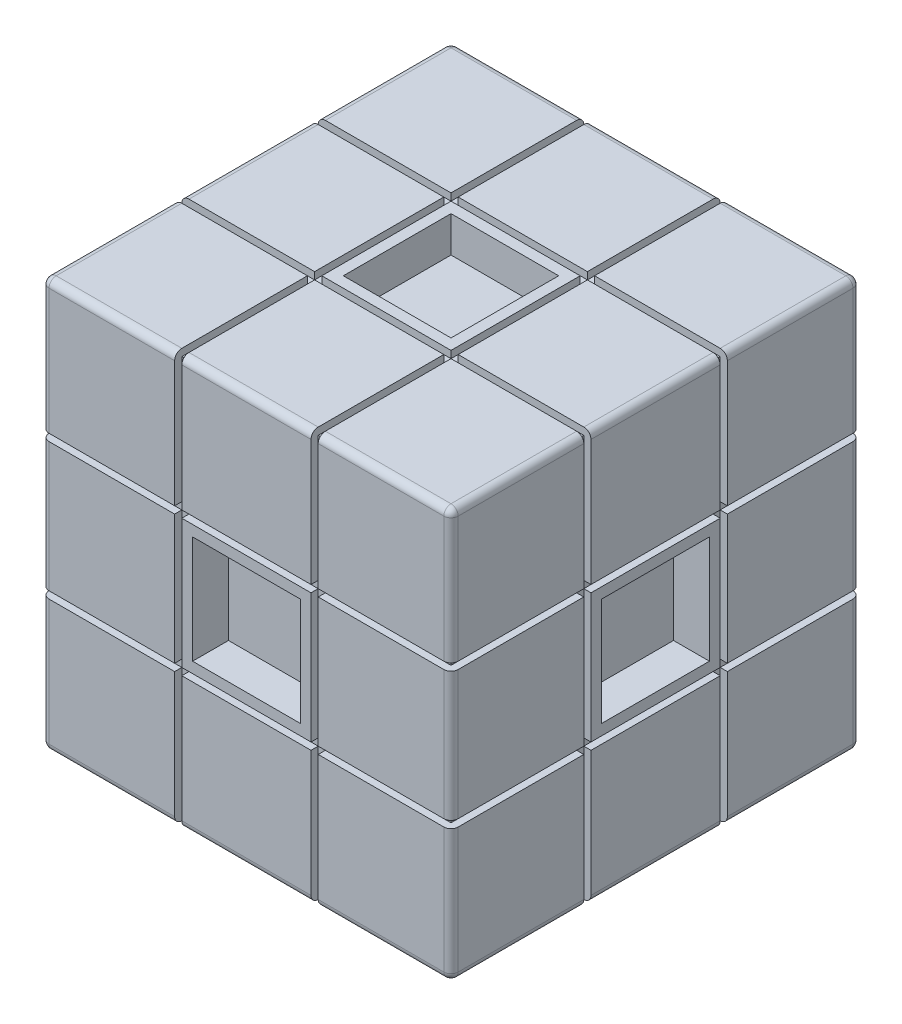
SolidWorks part; units mm, degrees
ref_plane "前视基准面" through (0, 0, 0) normal (0, 0, 1) x (1, 0, 0)
ref_plane "上视基准面" through (0, 0, 0) normal (0, 1, 0) x (1, 0, 0)
ref_plane "右视基准面" through (0, 0, 0) normal (1, 0, 0) x (0, 0, -1)
sketch "草图1" plane through (0, 0, 0) normal (0, 1, 0) x (1, 0, 0)
  line L0 (0, 0) -> (57, 0)
  line L1 (0, 0) -> (0, 57)
  line L2 (57, 0) -> (57, 57)
  line L3 (0, 57) -> (57, 57)
extrude "凸台-拉伸1" add sketch "草图1" along normal blind 57
sketch "草图2" plane through (0, 0, 0) normal (0, 1, 0) x (1, 0, 0)
  line L0 (36, 21) -> (36, 36)
  line L1 (36, 21) -> (21, 21)
  line L2 (36, 36) -> (21, 36)
  line L3 (21, 21) -> (21, 36)
  point P1 (28.5, 28.5)
extrude "切除-拉伸3" cut sketch "草图2" along normal blind 5
sketch "草图5" plane through (0, 0, 0) normal (0, 0, 1) x (1, 0, 0)
  line L0 (36, 36) -> (36, 21)
  line L1 (36, 36) -> (21, 36)
  line L2 (36, 21) -> (21, 21)
  line L3 (21, 36) -> (21, 21)
  point P1 (28.5, 28.5)
extrude "切除-拉伸4" cut sketch "草图5" against normal blind 5
sketch "草图6" plane through (0, 57, 0) normal (0, 1, 0) x (1, 0, 0)
  line L0 (36, 36) -> (36, 21)
  line L1 (36, 36) -> (21, 36)
  line L2 (36, 21) -> (21, 21)
  line L3 (21, 36) -> (21, 21)
extrude "切除-拉伸5" cut sketch "草图6" against normal blind 5
sketch "草图8" plane through (0, 0, -57) normal (0, 0, -1) x (-1, 0, 0)
  line L0 (-36, 21) -> (-36, 36)
  line L1 (-36, 21) -> (-21, 21)
  line L2 (-36, 36) -> (-21, 36)
  line L3 (-21, 21) -> (-21, 36)
extrude "切除-拉伸6" cut sketch "草图8" against normal blind 5
sketch "草图9" plane through (0, 0, 0) normal (-1, 0, 0) x (0, 0, 1)
  line L0 (-36, 36) -> (-21, 36)
  line L1 (-36, 36) -> (-36, 21)
  line L2 (-21, 36) -> (-21, 21)
  line L3 (-36, 21) -> (-21, 21)
extrude "切除-拉伸7" cut sketch "草图9" against normal blind 5
sketch "草图10" plane through (57, 0, 0) normal (1, 0, 0) x (0, 0, -1)
  line L0 (21, 36) -> (36, 36)
  line L1 (21, 36) -> (21, 21)
  line L2 (36, 36) -> (36, 21)
  line L3 (21, 21) -> (36, 21)
extrude "切除-拉伸8" cut sketch "草图10" against normal blind 5
sketch "草图12" plane through (0, 0, 0) normal (0, 0, 1) x (1, 0, 0)
  line L0 (38.5, 57) -> (38.5, 38.5)
  line L1 (0, 38.5) -> (0, 37.5)
  line L2 (0, 18.5) -> (0, 19.5)
  line L3 (57, 37.5) -> (57, 38.5)
  line L4 (57, 19.5) -> (57, 18.5)
  line L5 (37.5, 57) -> (37.5, 38.5)
  line L6 (57, 18.5) -> (38.5, 18.5)
  line L7 (37.5, 57) -> (38.5, 57)
  line L8 (38.5, 0) -> (37.5, 0)
  line L9 (18.5, 0) -> (19.5, 0)
  line L10 (19.5, 57) -> (18.5, 57)
  line L11 (19.5, 57) -> (19.5, 38.5)
  line L12 (18.5, 57) -> (18.5, 38.5)
  line L13 (18.5, 37.5) -> (0, 37.5)
  line L14 (57, 19.5) -> (38.5, 19.5)
  line L15 (57, 37.5) -> (38.5, 37.5)
  line L16 (57, 38.5) -> (38.5, 38.5)
  line L17 (18.5, 38.5) -> (0, 38.5)
  line L18 (18.5, 37.5) -> (18.5, 19.5)
  line L19 (19.5, 37.5) -> (19.5, 19.5)
  line L20 (37.5, 37.5) -> (37.5, 19.5)
  line L21 (38.5, 37.5) -> (38.5, 19.5)
  line L22 (37.5, 38.5) -> (19.5, 38.5)
  line L23 (37.5, 37.5) -> (19.5, 37.5)
  line L24 (38.5, 18.5) -> (38.5, 0)
  line L25 (37.5, 18.5) -> (37.5, 0)
  line L26 (37.5, 19.5) -> (19.5, 19.5)
  line L27 (37.5, 18.5) -> (19.5, 18.5)
  line L28 (18.5, 18.5) -> (18.5, 0)
  line L29 (19.5, 18.5) -> (19.5, 0)
  line L30 (18.5, 19.5) -> (0, 19.5)
  line L31 (18.5, 18.5) -> (0, 18.5)
extrude "切除-拉伸9" cut sketch "草图12" against normal blind 1
sketch "草图13" plane through (0, 0, 0) normal (0, 0, 1) x (1, 0, 0)
  line L0 (18.5, 57) -> (19.5, 57)
  line L1 (18.5, 57) -> (18.5, 56)
  line L2 (18.5, 57) -> (18.5, 38.5) construction
  line L3 (18.5, 56) -> (19.5, 56)
  line L4 (19.5, 38.5) -> (19.5, 57) construction
  line L5 (19.5, 56) -> (19.5, 57)
  line L9 (37.5, 56) -> (37.5, 57)
  line L10 (38.5, 56) -> (37.5, 56)
  line L11 (38.5, 57) -> (38.5, 56)
  line L12 (38.5, 57) -> (37.5, 57)
  line L15 (38.5, 0) -> (37.5, 0)
  line L16 (38.5, 0) -> (38.5, 1)
  line L17 (38.5, 1) -> (37.5, 1)
  line L18 (37.5, 1) -> (37.5, 0)
  line L19 (19.5, 1) -> (19.5, 0)
  line L20 (18.5, 1) -> (19.5, 1)
  line L21 (18.5, 0) -> (18.5, 1)
  line L22 (18.5, 0) -> (19.5, 0)
  line L23 (0, 18.5) -> (0, 19.5)
  line L24 (0, 18.5) -> (1, 18.5)
  line L25 (1, 18.5) -> (1, 19.5)
  line L26 (1, 19.5) -> (0, 19.5)
  line L27 (1, 37.5) -> (0, 37.5)
  line L28 (1, 38.5) -> (1, 37.5)
  line L29 (0, 38.5) -> (1, 38.5)
  line L30 (0, 38.5) -> (0, 37.5)
  line L31 (57, 38.5) -> (57, 37.5)
  line L32 (57, 38.5) -> (56, 38.5)
  line L33 (56, 38.5) -> (56, 37.5)
  line L34 (56, 37.5) -> (57, 37.5)
  line L35 (56, 19.5) -> (57, 19.5)
  line L36 (56, 18.5) -> (56, 19.5)
  line L37 (57, 18.5) -> (56, 18.5)
  line L38 (57, 18.5) -> (57, 19.5)
extrude "切除-拉伸10" cut sketch "草图13" against normal through all
sketch "草图14" plane through (0, 0, 0) normal (-1, 0, 0) x (0, 0, 1)
  line L0 (-57, 37.5) -> (-57, 38.5)
  line L1 (-57, 37.5) -> (-56, 37.5)
  line L2 (-57, 38.5) -> (-56, 38.5)
  line L3 (-56, 37.5) -> (-56, 38.5)
  line L7 (-56, 19.5) -> (-56, 18.5)
  line L8 (-57, 18.5) -> (-56, 18.5)
  line L9 (-57, 19.5) -> (-56, 19.5)
  line L10 (-57, 19.5) -> (-57, 18.5)
  line L11 (-19.5, 57) -> (-18.5, 57)
  line L12 (-19.5, 57) -> (-19.5, 56)
  line L13 (-18.5, 57) -> (-18.5, 56)
  line L14 (-19.5, 56) -> (-18.5, 56)
  line L15 (-37.5, 56) -> (-38.5, 56)
  line L16 (-38.5, 57) -> (-38.5, 56)
  line L17 (-37.5, 57) -> (-37.5, 56)
  line L18 (-37.5, 57) -> (-38.5, 57)
  line L19 (-37.5, 0) -> (-38.5, 0)
  line L20 (-37.5, 0) -> (-37.5, 1)
  line L21 (-38.5, 0) -> (-38.5, 1)
  line L22 (-37.5, 1) -> (-38.5, 1)
  line L23 (-19.5, 1) -> (-18.5, 1)
  line L24 (-18.5, 0) -> (-18.5, 1)
  line L25 (-19.5, 0) -> (-19.5, 1)
  line L26 (-19.5, 0) -> (-18.5, 0)
  line L27 (-1, 37.5) -> (-1, 38.5)
  line L28 (0, 38.5) -> (-1, 38.5)
  line L29 (0, 37.5) -> (-1, 37.5)
  line L30 (0, 37.5) -> (0, 38.5)
  line L31 (0, 19.5) -> (0, 18.5)
  line L32 (0, 19.5) -> (-1, 19.5)
  line L33 (0, 18.5) -> (-1, 18.5)
  line L34 (-1, 19.5) -> (-1, 18.5)
extrude "切除-拉伸11" cut sketch "草图14" against normal through all
sketch "草图15" plane through (0, 57, 0) normal (0, 1, 0) x (1, 0, 0)
  line L0 (0, 18.5) -> (0, 19.5)
  line L1 (0, 18.5) -> (1, 18.5)
  line L2 (0, 19.5) -> (1, 19.5)
  line L3 (1, 18.5) -> (1, 19.5)
  line L7 (1, 38.5) -> (1, 37.5)
  line L8 (0, 37.5) -> (1, 37.5)
  line L9 (0, 38.5) -> (1, 38.5)
  line L10 (0, 38.5) -> (0, 37.5)
  line L13 (57, 38.5) -> (57, 37.5)
  line L14 (57, 38.5) -> (56, 38.5)
  line L15 (57, 37.5) -> (56, 37.5)
  line L16 (56, 38.5) -> (56, 37.5)
  line L17 (56, 18.5) -> (56, 19.5)
  line L18 (57, 19.5) -> (56, 19.5)
  line L19 (57, 18.5) -> (56, 18.5)
  line L20 (57, 18.5) -> (57, 19.5)
extrude "切除-拉伸12" cut sketch "草图15" against normal through all
sketch "草图16" plane through (0, 0, 0) normal (0, -1, 0) x (1, 0, 0)
  line L0 (18.5, -57) -> (19.5, -57)
  line L1 (18.5, -57) -> (18.5, -56)
  line L2 (19.5, -57) -> (19.5, -56)
  line L3 (18.5, -56) -> (19.5, -56)
  line L4 (18.5, -57) -> (0, -57) construction
  line L5 (18.5, -57) -> (18.5, -38.5) construction
  line L9 (38.5, -56) -> (37.5, -56)
  line L10 (37.5, -57) -> (37.5, -56)
  line L11 (38.5, -57) -> (38.5, -56)
  line L12 (38.5, -57) -> (37.5, -57)
extrude "切除-拉伸13" cut sketch "草图16" against normal through all
fillet "圆角3" radius 1 9 edges at (57, 47.75, 0) (57, 9.25, 0) (57, 28.5, 0) (57, 0, -47.75) (57, 0, -9.25) (57, 0, -28.5) (47.75, 0, 0) (28.5, 0, 0) (9.25, 0, 0)
fillet "圆角4" radius 1 17 edges at (56.7071, 0.2929, -57) (0, 9.75, 0) (0, 0.2929, -0.2929) (0, 28.5, 0) (0, 47.75, 0) (57, 47.75, -57) (57, 28.5, -57) (57, 9.75, -57) (47.25, 0, -57) (28.5, 0, -57) (9.25, 0, -57) (0, 0, -47.75) (0, 0, -28.5) (0, 0, -9.75) (0, 9.25, -57) (0, 28.5, -57) (0, 47.75, -57)
fillet "圆角5" radius 1 16 edges at (9.75, 57, -57) (0.2929, 57, -56.7071) (47.25, 57, -57) (56.7071, 57, -56.7071) (0, 57, -9.75) (0.2929, 57, -0.2929) (57, 57, -9.75) (56.7071, 57, -0.2929) (0, 57, -47.25) (0, 57, -28.5) (28.5, 57, -57) (57, 57, -47.25) (57, 57, -28.5) (9.75, 57, 0) (28.5, 57, 0) (47.25, 57, 0)
